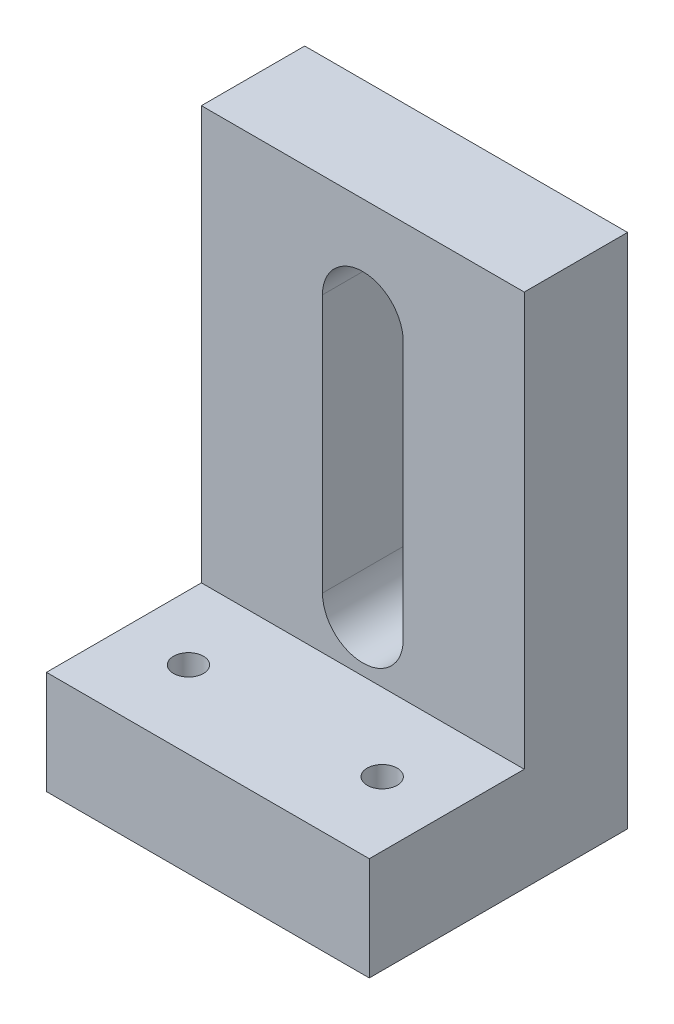
SolidWorks part; units mm, degrees
material "Delrin 2700 NC010, Low Viscosity Acetal Copolymer (SS)"
ref_plane "Front Plane" through (0, 0, 0) normal (0, 0, 1) x (1, 0, 0)
ref_plane "Top Plane" through (0, 0, 0) normal (0, 1, 0) x (1, 0, 0)
ref_plane "Right Plane" through (0, 0, 0) normal (1, 0, 0) x (0, 0, -1)
sketch "Sketch3" plane through (0, 0, 0) normal (1, 0, 0) x (0, 0, -1)
  line L0 (0, 0) -> (25.4, 0)
  line L1 (25.4, 0) -> (25.4, 50.8)
  line L2 (25.4, 50.8) -> (15.24, 50.8)
  line L3 (15.24, 50.8) -> (15.24, 10.16)
  line L4 (15.24, 10.16) -> (0, 10.16)
  line L5 (0, 10.16) -> (0, 0)
  dimension "D1" = 10.16
  dimension "D2" = 25.4
  dimension "D3" = 50.8
  dimension "D4" = 10.16
extrude "Boss-Extrude1" add sketch "Sketch3" against normal blind 31.75
sketch "Sketch4" plane through (0, 0, -15.24) normal (0, 0, 1) x (1, 0, 0)
  line L0 (-15.875, 40.64) -> (-15.875, 15.24)
  line L3 (-31.75, 10.16) -> (0, 10.16) construction
  line L5 (-31.75, 50.8) -> (0, 50.8) construction
  line L7 (-11.9062, 40.64) -> (-11.9062, 15.24)
  line L8 (-19.8438, 40.64) -> (-19.8437, 15.24)
  circle A0 centre (-15.875, 40.64) radius 3.9688
  circle A1 centre (-15.875, 15.24) radius 3.9688
  point P12 (-15.875, 50.8)
  dimension "D3" = 7.9375
  dimension "D1" = 25.4
  dimension "D2" = 5.08
extrude "Cut-Extrude1" cut sketch "Sketch4" against normal through all
sketch "Sketch5" plane through (0, 10.16, 0) normal (0, 1, 0) x (1, 0, 0)
  line L0 (-31.75, 15.24) -> (-31.75, 0) construction
  line L1 (-31.75, 0) -> (0, 0) construction
  circle A0 centre (-25.4, 7.62) radius 1.4732
  circle A1 centre (-6.35, 7.62) radius 1.4732
  point P8 (-31.75, 7.62)
  dimension "D3" = 2.9464
  dimension "D1" = 6.35
  dimension "D2" = 19.05
  dimension "D4" = 7.62
extrude "Cut-Extrude2" cut sketch "Sketch5" against normal through all
